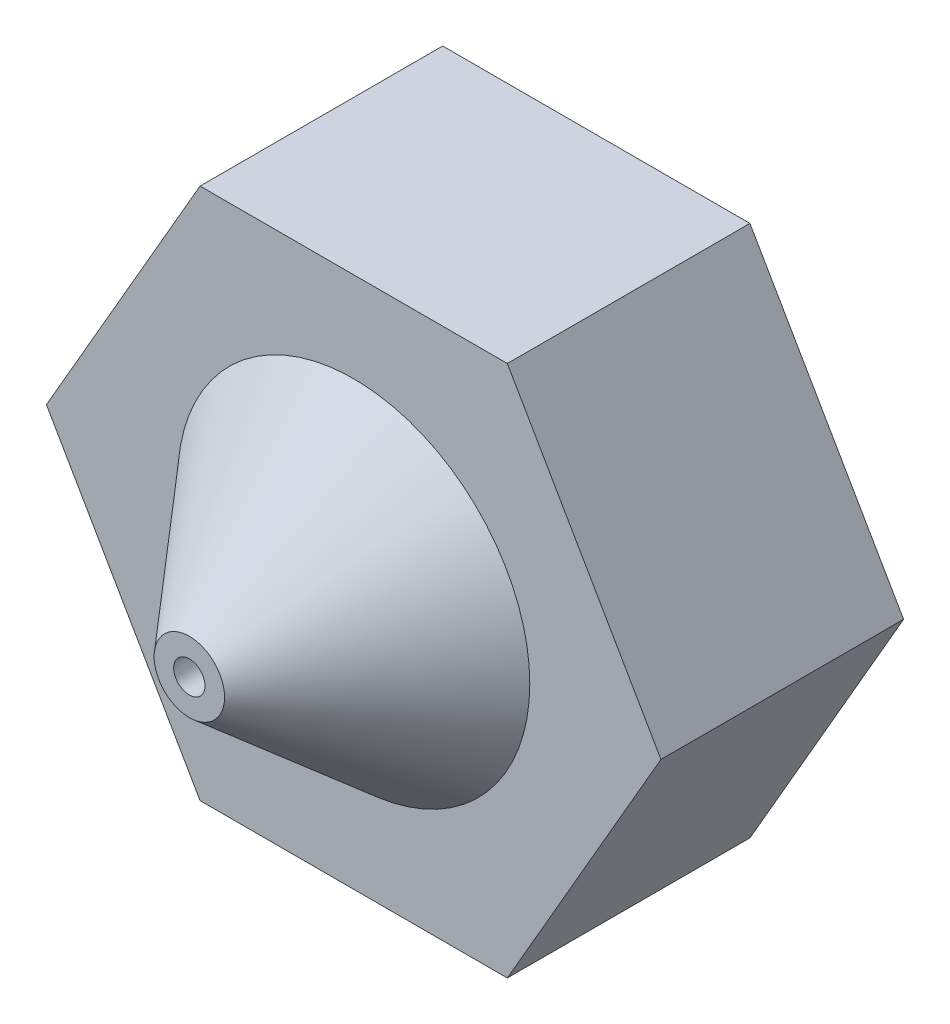
SolidWorks part; units mm, degrees
material "Latão"
ref_plane "Plano frontal" through (0, 0, 0) normal (0, 0, 1) x (1, 0, 0)
ref_plane "Plano superior" through (0, 0, 0) normal (0, 1, 0) x (1, 0, 0)
ref_plane "Plano direito" through (0, 0, 0) normal (1, 0, 0) x (0, 0, -1)
sketch "Esboço1" plane through (0, 0, 0) normal (0, 0, 1) x (1, 0, 0)
  line L0 (-0.5, 0) -> (-10.7, 0) construction
  line L1 (-3.637, 1.6) -> (-1.674, 5)
  line L2 (-1.674, 5) -> (-3.637, 8.4)
  line L3 (-3.637, 8.4) -> (-7.563, 8.4)
  line L4 (-7.563, 8.4) -> (-9.526, 5)
  line L5 (-9.526, 5) -> (-7.563, 1.6)
  line L6 (-7.563, 1.6) -> (-3.637, 1.6)
  circle A0 centre (-5.6, 5) radius 3.4 construction
  dimension "D1" = 6.8
extrude "Ressalto-extrusão1" add sketch "Esboço1" along normal blind 3.1
ref_plane "Plano1" through (0, 0, 5.2) normal (0, 0, 1) x (1, 0, 0)
sketch "Esboço2" plane through (0, 0, 5.2) normal (0, 0, 1) x (1, 0, 0)
  circle A0 centre (-5.6, 5) radius 0.45
  dimension "D1" = 0.9
sketch "Esboço3" plane through (0, 0, 3.1) normal (0, 0, 1) x (1, 0, 0)
  circle A0 centre (-5.6, 5) radius 2.25
  dimension "D1" = 4.5
sketch3d "3DSketch1"
  line L0 (-5.6, 5, 3.1) -> (-5.6, 5, 5.2)
loft "Loft3" add profiles "Esboço3", "Esboço2"
sketch "Esboço4" plane through (0, 0, 5.2) normal (0, 0, 1) x (1, 0, 0)
  circle A0 centre (-5.6, 5) radius 0.2
  dimension "D1" = 0.4
extrude "Corte-extrusão1" cut sketch "Esboço4" against normal through all
